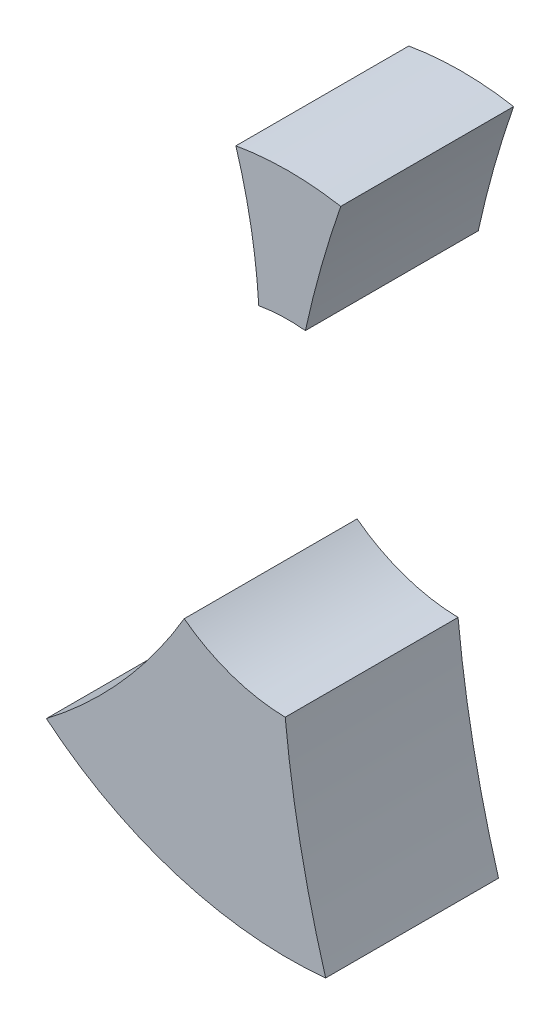
SolidWorks part; units mm, degrees
ref_plane "Front Plane" through (0, 0, 0) normal (0, 0, 1) x (1, 0, 0)
ref_plane "Top Plane" through (0, 0, 0) normal (0, 1, 0) x (1, 0, 0)
ref_plane "Right Plane" through (0, 0, 0) normal (1, 0, 0) x (0, 0, -1)
sketch "Sketch1" plane through (0, 0, 0) normal (0, 0, 1) x (1, 0, 0)
  circle A0 centre (0, 0) radius 6
  circle A1 centre (0, 0) radius 13.2
extrude "Boss-Extrude1" add sketch "Sketch1" along normal blind 6
sketch "Sketch2" plane through (0, 0, 6) normal (0, 0, 1) x (1, 0, 0)
  line L0 (0, 0) -> (0, 15.2) construction
  line L1 (-1.8199, 15.2) -> (0, 0) construction
  line L2 (1.8199, 15.2) -> (0, 0) construction
  arc A0 (-1.1225, 7) -> (0.8428, 7.0392) centre (0, 0) ccw
  arc A1 (-2.8199, 12.8953) -> (2.8199, 12.8953) centre (0, 0) cw
  arc A2 (-1.8199, 10.32) -> (1.8199, 10.32) centre (0, 0) cw
  arc A3 (-2.8199, 12.8953) -> (-1.8199, 10.32) centre (-19.8561, 4.7982) ccw
  arc A4 (2.8199, 12.8953) -> (1.8199, 10.32) centre (37.9293, -2.2197) cw
extrude "Cut-Extrude1" cut sketch "Sketch2" against normal through all contours A1 A4 A2 A3
